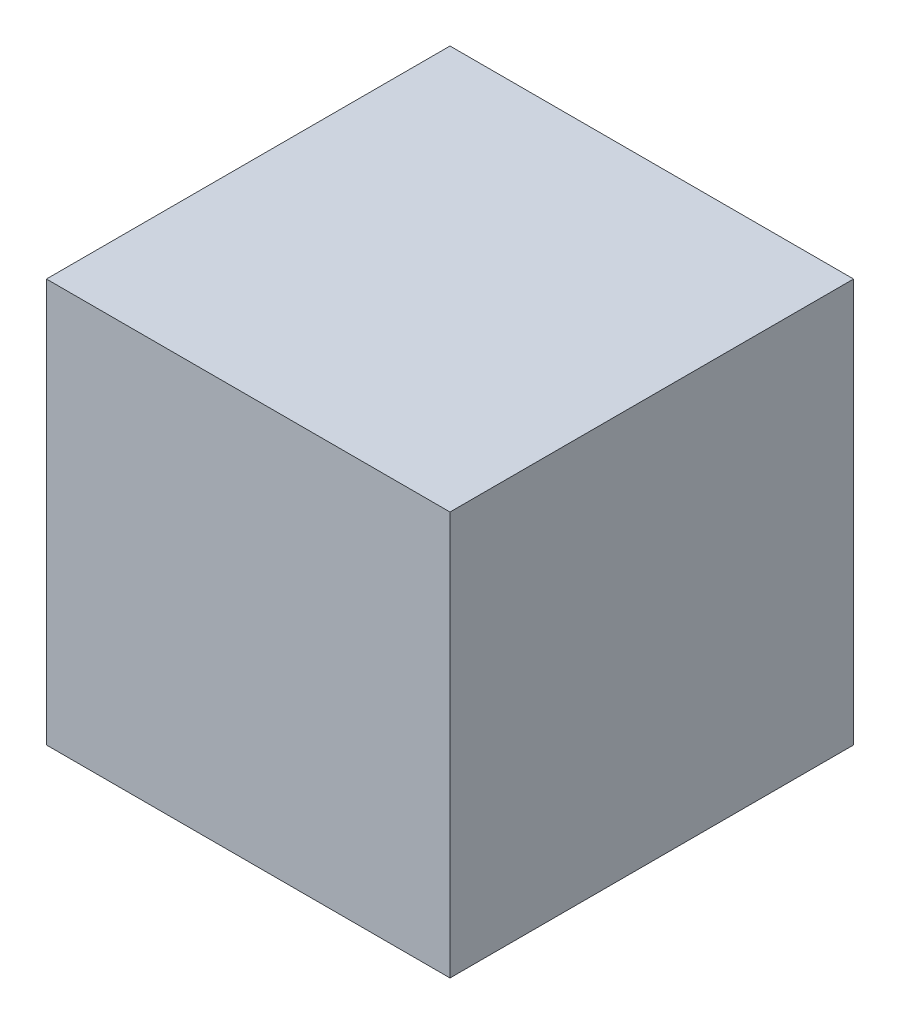
SolidWorks part; units mm, degrees
ref_plane "前视基准面" through (0, 0, 0) normal (0, 0, 1) x (1, 0, 0)
ref_plane "上视基准面" through (0, 0, 0) normal (0, 1, 0) x (1, 0, 0)
ref_plane "右视基准面" through (0, 0, 0) normal (1, 0, 0) x (0, 0, -1)
sketch "草图4" plane through (0, 0, 0) normal (0, 0, 1) x (1, 0, 0)
  line L1 (-50, 50) -> (50, 50)
  line L2 (-50, 50) -> (-50, -50)
  line L3 (-50, -50) -> (50, -50)
  line L4 (50, 50) -> (50, -50)
  line L5 (-50, 50) -> (50, -50) construction
  line L6 (-50, -50) -> (50, 50) construction
  point P0 (0, 0)
  dimension "D1" = 100
  dimension "D2" = 100
extrude "凸台-拉伸1" add sketch "草图4" along normal mid plane 100
